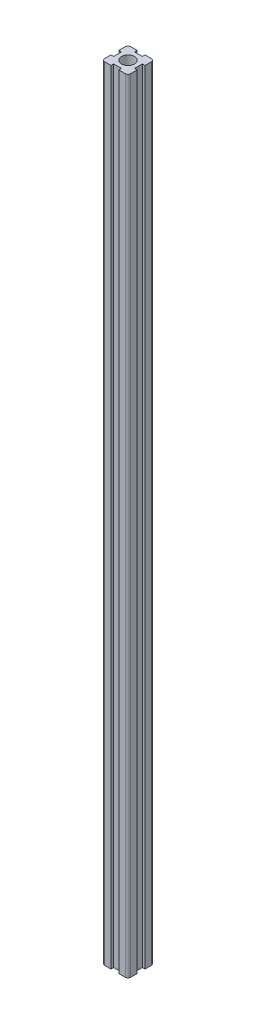
SolidWorks part; units mm, degrees
ref_plane "Front Plane" through (0, 0, 0) normal (0, 0, 1) x (1, 0, 0)
ref_plane "Top Plane" through (0, 0, 0) normal (0, 1, 0) x (1, 0, 0)
ref_plane "Right Plane" through (0, 0, 0) normal (1, 0, 0) x (0, 0, -1)
sketch "Sketch1" plane through (0, 0, 0) normal (0, 1, 0) x (1, 0, 0)
  line L1 (-10, 10) -> (10, 10)
  line L2 (-10, 10) -> (-10, -10)
  line L3 (-10, -10) -> (10, -10)
  line L4 (10, 10) -> (10, -10)
  line L5 (-10, 10) -> (10, -10) construction
  line L6 (-10, -10) -> (10, 10) construction
  circle A0 centre (0, 0) radius 5
  point P0 (0, 0)
  dimension "D1" = 20
  dimension "D2" = 20
extrude "Boss-Extrude2" add sketch "Sketch1" along normal mid plane 600
sketch "Sketch2" plane through (0, -300, 0) normal (0, -1, 0) x (1, 0, 0)
  line L0 (-10, 10) -> (10, 10) construction
  line L1 (-3, 12) -> (3, 12)
  line L2 (-3, 12) -> (-3, 8)
  line L3 (-3, 8) -> (3, 8)
  line L4 (3, 12) -> (3, 8)
  line L5 (-3, 12) -> (3, 8) construction
  line L6 (-3, 8) -> (3, 12) construction
  line L7 (10, 10) -> (10, -10) construction
  line L8 (8, 3) -> (12, 3)
  line L9 (8, 3) -> (8, -3)
  line L10 (8, -3) -> (12, -3)
  line L11 (12, 3) -> (12, -3)
  line L12 (8, 3) -> (12, -3) construction
  line L13 (8, -3) -> (12, 3) construction
  line L14 (10, -10) -> (-10, -10) construction
  line L15 (-3, -8) -> (3, -8)
  line L16 (-3, -8) -> (-3, -12)
  line L17 (-3, -12) -> (3, -12)
  line L18 (3, -8) -> (3, -12)
  line L19 (-3, -8) -> (3, -12) construction
  line L20 (-3, -12) -> (3, -8) construction
  line L21 (-10, -10) -> (-10, 10) construction
  line L22 (-12, 3) -> (-8, 3)
  line L23 (-12, 3) -> (-12, -3)
  line L24 (-12, -3) -> (-8, -3)
  line L25 (-8, 3) -> (-8, -3)
  line L26 (-12, 3) -> (-8, -3) construction
  line L27 (-12, -3) -> (-8, 3) construction
  point P0 (0, 10)
  point P7 (10, 0)
  point P14 (0, -10)
  point P21 (-10, 0)
  dimension "D1" = 6
  dimension "D2" = 6
  dimension "D3" = 6
  dimension "D4" = 6
  dimension "D5" = 4
  dimension "D6" = 4
  dimension "D7" = 4
  dimension "D8" = 4
extrude "Cut-Extrude1" cut sketch "Sketch2" against normal blind 600
fillet "Fillet1" radius 2 4 edges at (10, 0, 10) (10, 0, -10) (-10, 0, 10) (-10, 0, -10)
